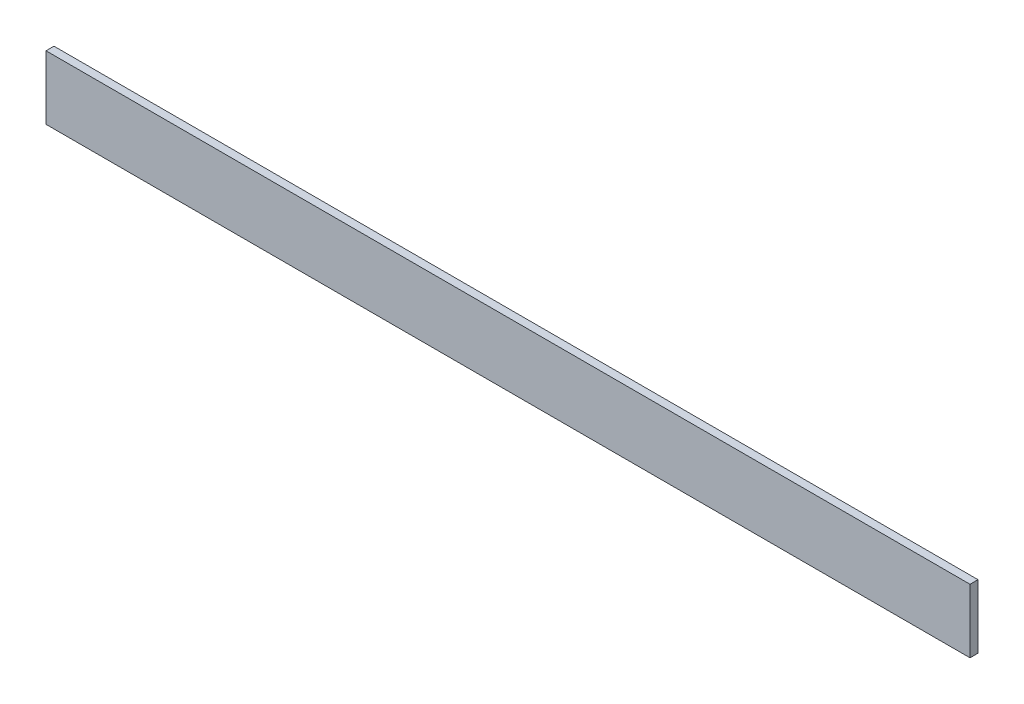
SolidWorks part; units mm, degrees
ref_plane "Plan de face" through (0, 0, 0) normal (0, 0, 1) x (1, 0, 0)
ref_plane "Plan de dessus" through (0, 0, 0) normal (0, 1, 0) x (1, 0, 0)
ref_plane "Plan de droite" through (0, 0, 0) normal (1, 0, 0) x (0, 0, -1)
sketch "Esquisse1" plane through (0, 0, 0) normal (0, 0, 1) x (1, 0, 0)
  line L1 (-290, -20) -> (290, -20)
  line L2 (-290, -20) -> (-290, 20)
  line L3 (-290, 20) -> (290, 20)
  line L4 (290, -20) -> (290, 20)
  line L5 (-290, -20) -> (290, 20) construction
  line L6 (-290, 20) -> (290, -20) construction
  point P0 (0, 0)
  dimension "D1" = 580
  dimension "D2" = 40
extrude "Boss.-Extru.1" add sketch "Esquisse1" along normal blind 5
